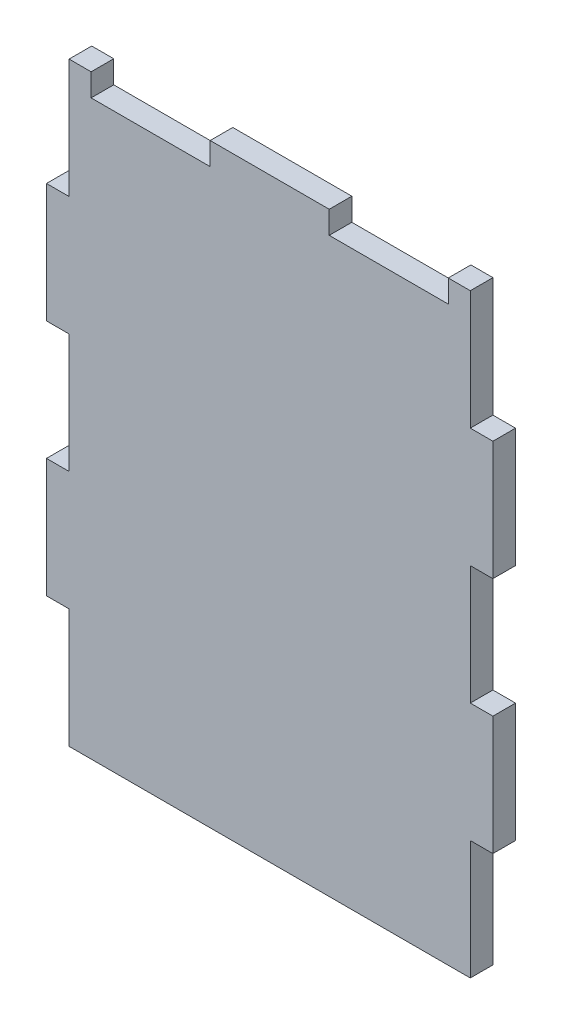
SolidWorks part; units mm, degrees
material "1060 Alloy"
ref_plane "Front Plane" through (0, 0, 0) normal (0, 0, 1) x (1, 0, 0)
ref_plane "Top Plane" through (0, 0, 0) normal (0, 1, 0) x (1, 0, 0)
ref_plane "Right Plane" through (0, 0, 0) normal (1, 0, 0) x (0, 0, -1)
sketch "Sketch1" plane through (0, 0, 0) normal (0, 0, 1) x (1, 0, 0)
  line L0 (0, 76.2) -> (0, 101.6)
  line L1 (4.826, 0) -> (90.424, 0)
  line L2 (0, 25.4) -> (0, 50.8)
  line L3 (4.826, 127) -> (90.424, 127)
  line L4 (95.25, 25.4) -> (95.25, 50.8)
  line L6 (0, 0) -> (95.25, 0) construction
  line L7 (0, 101.6) -> (4.826, 101.6)
  line L8 (4.826, 127) -> (4.826, 101.6)
  line L9 (0, 25.4) -> (4.826, 25.4)
  line L10 (0, 0) -> (0, 127) construction
  line L12 (4.826, 25.4) -> (4.826, 0)
  line L13 (0, 76.2) -> (4.826, 76.2)
  line L15 (0, 50.8) -> (4.826, 50.8)
  line L16 (4.826, 76.2) -> (4.826, 50.8)
  line L18 (90.424, 127) -> (90.424, 101.6)
  line L19 (90.424, 101.6) -> (95.25, 101.6)
  line L21 (95.25, 76.2) -> (90.424, 76.2)
  line L23 (95.25, 50.8) -> (90.424, 50.8)
  line L24 (90.424, 76.2) -> (90.424, 50.8)
  line L25 (95.25, 25.4) -> (90.424, 25.4)
  line L28 (90.424, 25.4) -> (90.424, 0)
  line L29 (95.25, 76.2) -> (95.25, 101.6)
  line L30 (0, 127) -> (95.25, 127) construction
  line L31 (95.25, 0) -> (95.25, 127) construction
  dimension "D1" = 95.25
  dimension "D2" = 127
  dimension "D3" = 4.826
extrude "Boss-Extrude1" add sketch "Sketch1" along normal blind 4.826
sketch "Sketch2" plane through (0, 127, 0) normal (0, 1, 0) x (1, 0, 0)
  line L0 (60.325, -2.413) -> (34.925, -2.413) construction
  line L1 (34.925, -4.826) -> (9.525, -4.826)
  line L2 (34.925, -4.826) -> (34.925, 0)
  line L3 (34.925, 0) -> (9.525, 0)
  line L4 (90.424, 0) -> (4.826, 0)
  line L5 (4.826, 0) -> (4.826, -4.826)
  line L6 (4.826, -4.826) -> (90.424, -4.826)
  line L7 (90.424, -4.826) -> (90.424, 0)
  line L8 (90.424, 0) -> (4.826, 0)
  line L9 (4.826, 0) -> (4.826, -4.826)
  line L10 (4.826, -4.826) -> (90.424, -4.826)
  line L11 (90.424, -4.826) -> (90.424, 0)
  line L12 (9.525, -4.826) -> (9.525, 0)
  line L13 (60.325, -4.826) -> (85.725, -4.826)
  line L14 (60.325, -4.826) -> (60.325, 0)
  line L15 (60.325, 0) -> (85.725, 0)
  line L16 (85.725, -4.826) -> (85.725, 0)
  line L17 (47.625, -2.413) -> (47.625, 0) construction
  line M12 (90.424, 0) -> (4.826, 0)
  line M14 (4.826, -4.826) -> (90.424, -4.826)
  dimension "D2" = 25.4
  dimension "D3" = 25.4
  dimension "D4" = 25.4
  dimension "D1" = 0
extrude "Cut-Extrude1" cut sketch "Sketch2" against normal blind 4.826 contours L10 L16 L8 L14 | L12 L2 M14 M12
equation "\"sheet width\"= .19"
equation "\"width\"= 24.5"
equation "\"length\"= 34.5"
equation "\"standoff hole size\"= .5"
equation "\"ground clearence\"= 3"
equation "\"small drive pulley\"= 74.55mm"
equation "\"large drive pulley\"= 150.95mm"
equation "\"drive axle hole size\"= .5"
equation "\"front pulley clearence\"= 1"
equation "\"center support location\"= 19"
equation "\"inner to outer wall size\"= 3.75"
equation "\"D1@Sketch1\"=\"inner to outer wall size\""
equation "\"D3@Sketch1\"=\"sheet width\""
equation "\"D1@Boss-Extrude1\"=\"sheet width\""
equation "\"D1@Cut-Extrude1\"=\"sheet width\""
